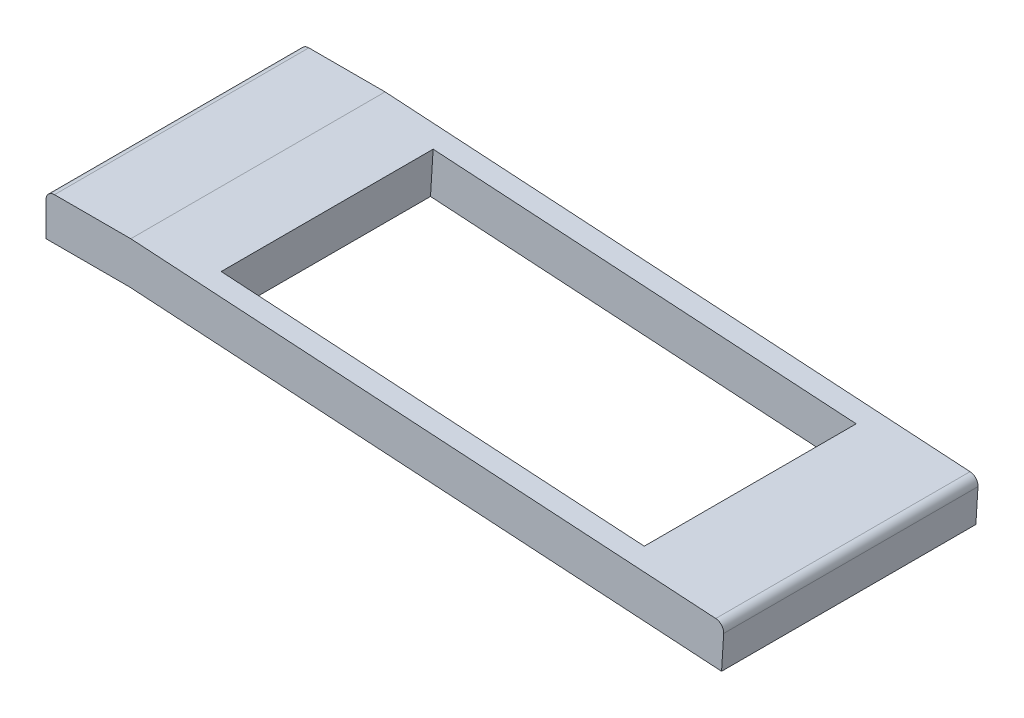
SolidWorks part; units mm, degrees
ref_plane "Front Plane" through (0, 0, 0) normal (0, 0, 1) x (1, 0, 0)
ref_plane "Top Plane" through (0, 0, 0) normal (0, 1, 0) x (1, 0, 0)
ref_plane "Right Plane" through (0, 0, 0) normal (1, 0, 0) x (0, 0, -1)
sketch "Sketch2" plane through (0, 0, 0) normal (0, 0, 1) x (1, 0, 0)
  line L0 (0.1, 0) -> (1, 0)
  line L1 (1, 0) -> (7.9002, -0.4295)
  line L2 (0, -0.5) -> (0.9845, -0.5)
  line L3 (0.9845, -0.5) -> (7.9689, -0.9348)
  line L4 (0, -0.1) -> (0, -0.5)
  line L5 (7.9938, -0.5355) -> (7.9689, -0.9348)
  line L6 (0, 0) -> (1, 0) construction
  line L7 (1, 0) -> (8, -0.4357) construction
  arc A0 (0, -0.1) -> (0.1, 0) centre (0.1, -0.1) cw
  arc A1 (7.9002, -0.4295) -> (7.9938, -0.5355) centre (7.894, -0.5293) cw
  point P10 (0, 0)
  point P14 (8, -0.4357)
  dimension "D3" = 0.1
  dimension "D4" = 0.1
  dimension "D1" = 1
  dimension "D2" = 7
extrude "Boss-Extrude3" add sketch "Sketch2" along normal blind 3
sketch "Sketch3" plane through (0.0039, 0.062, 0) normal (0.0621, 0.9981, 0) x (0.9981, -0.0621, 0)
  line L1 (1.8171, -0.2508) -> (6.8171, -0.2508)
  line L2 (1.8171, -0.2508) -> (1.8171, -2.7508)
  line L3 (1.8171, -2.7508) -> (6.8171, -2.7508)
  line L4 (6.8171, -0.2508) -> (6.8171, -2.7508)
  line L5 (1.8171, -0.2508) -> (6.8171, -2.7508) construction
  line L6 (1.8171, -2.7508) -> (6.8171, -0.2508) construction
  point P0 (4.3171, -1.5008)
  dimension "D1" = 5
  dimension "D2" = 2.5
extrude "Cut-Extrude1" cut sketch "Sketch3" against normal blind 3
